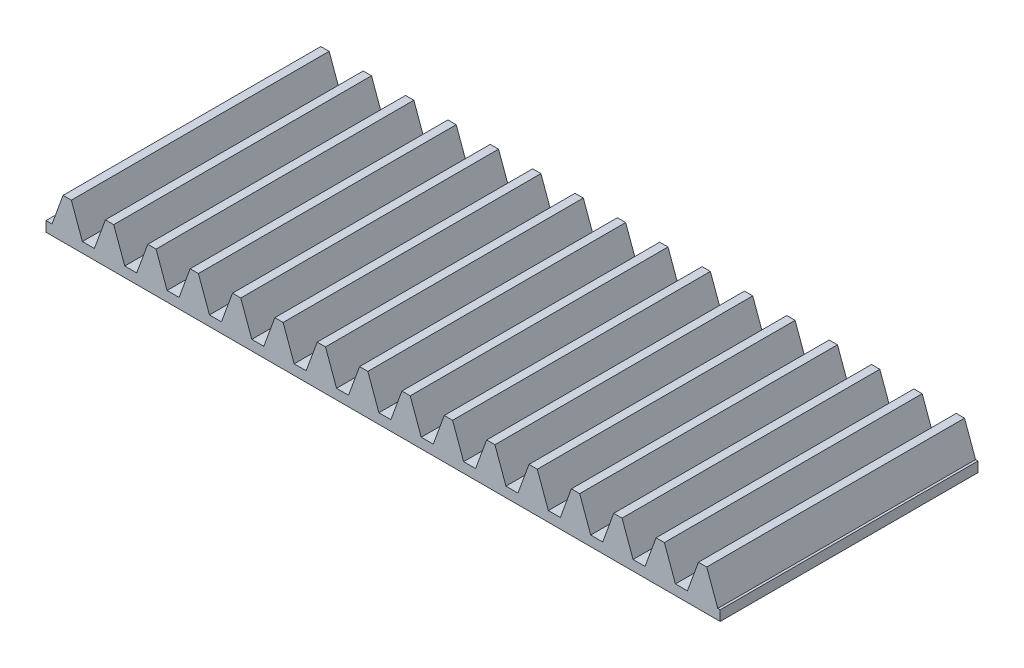
SolidWorks part; units mm, degrees
extrude "Blank" add sketch "BlankSke" against normal blind 19.12
sketch "BlankSke" plane through (0, 0, 0) normal (0, 0, 1) x (1, 0, 0)
  line L1 (0, 0) -> (50, 0)
  line L2 (0, 0) -> (0, 3)
  line L3 (0, 3) -> (50, 3)
  line L4 (50, 0) -> (50, 3)
  dimension "Length" = 50
  dimension "Blank_height" = 3
ref_plane "Plane1" through (0, 0, 0) normal (0, 0, 1) x (1, 0, 0)
ref_plane "Plane2" through (0, 0, 0) normal (0, 1, 0) x (1, 0, 0)
ref_plane "Plane3" through (0, 0, 0) normal (1, 0, 0) x (0, 0, -1)
sketch "HoldingSke" plane through (0, 0, 0) normal (0, 1, 0) x (1, 0, 0)
  line L0 (0, 0) -> (0.1392, 0.9903)
  line L1 (-15, 0) -> (100, 0) construction
  line L2 (0, 0) -> (-2.1039, 2.3779)
  line L3 (0, 0) -> (-11.863, 4.5341)
  line L4 (0, 0) -> (8.2587, 2.5249)
  line L5 (0, 0) -> (-23.7986, -8.8762)
  line L6 (0, 0) -> (-10.5278, -7.1032)
  line L9 (-71.009, 38.7566) -> (-24.0243, 55.8576)
  line L10 (-76.2, 3.3779) -> (-74.2, 3.3779)
  line L11 (0, 0) -> (-19.12, 0)
  line L12 (-76.2, 101.6) -> (-76.162, 101.6)
  line L13 (24.9733, 27.94) -> (52.9518, 28.4284)
  line L14 (24.9733, 27.94) -> (24.9743, 27.94)
  line L15 (24.9733, 27.94) -> (100.4006, 29.5858)
  circle A0 centre (0, 0) radius 19.05
  circle A1 centre (0, 0) radius 1
  circle A2 centre (0, 0) radius 12.7
  dimension "MPH" = 2
  dimension "Diameter" = 38.1
  dimension "Num_teeth" = 17
  dimension "Pitch" = 1
  dimension "Show_teeth" = 998
  dimension "Thickness" = 12.7
  dimension "Ap" = 20
  dimension "Pitch_height" = 2
  dimension "Width" = 19.12
  dimension "Backlash" = 0.038
  dimension "Addendum_fac" = 1
  dimension "Dedendum_fac" = 1.25
  dimension "Clearance_fac" = 0.25
  dimension "Dedendum_add" = 0.001
  dimension "Length" = 50
  dimension "Module" = 1
sketch "TooCutSkeIll" plane through (0, 0, 0) normal (0, 0, 1) x (1, 0, 0)
  line L0 (-1.2538, 2.9737) -> (-0.5045, 0.9152)
  line L1 (-0.2687, 0.75) -> (0.2687, 0.75)
  line L2 (0.5045, 0.9152) -> (1.2538, 2.9737)
  line L3 (50, 3) -> (0, 3) construction
  line L4 (0, 0) -> (0, 64.897) construction
  line L5 (-13.208, 2) -> (12.954, 2) construction
  line L6 (0, 0) -> (50, 0) construction
  line L7 (0.8994, 2) -> (0.8994, 48.7463) construction
  line L8 (-0.8994, 2) -> (-0.8994, 48.7463) construction
  line L9 (1.2914, 3) -> (1.2914, 3.0254)
  line L10 (-1.2914, 3) -> (-1.2914, 3.0254)
  line L11 (-1.2914, 3.0254) -> (1.2914, 3.0254)
  arc A0 (0.2687, 0.75) -> (0.5045, 0.9152) centre (0.2687, 1.001) ccw
  arc A1 (-0.5045, 0.9152) -> (-0.2687, 0.75) centre (-0.2687, 1.001) ccw
  arc A2 (1.2914, 3) -> (1.2538, 2.9737) centre (1.2914, 2.96) ccw
  arc A3 (-1.2538, 2.9737) -> (-1.2914, 3) centre (-1.2914, 2.96) ccw
  dimension "Pitch_height" = 2
  dimension "Addendum_plus" = 1.0254
  dimension "Pressure_angle" = 20
  dimension "Gap_width" = 1.7988
  dimension "Dedendum" = 1.25
extrude "ToothCutIll" [suppressed] cut sketch "TooCutSkeIll" against normal through all
sketch "TooCutSkeSim" plane through (0, 0, 0) normal (0, 0, 1) x (1, 0, 0)
  line L0 (0.4444, 0.75) -> (-0.4444, 0.75)
  line L1 (1.2726, 3.0254) -> (0.4444, 0.75)
  line L2 (0, 17.4625) -> (0, 53.467) construction
  line L3 (1.2726, 3.0254) -> (-1.2726, 3.0254)
  line L6 (-1.2726, 3.0254) -> (-0.4444, 0.75)
  line L9 (-0.8994, 2) -> (0.8994, 2) construction
  line L10 (0, 0) -> (50, 0) construction
  line L11 (0.8994, 2) -> (0.8994, 53.467) construction
  line L12 (-0.8994, 2) -> (-0.8994, 53.467) construction
  dimension "Pitch_height" = 2
  dimension "Addendum_plus" = 1.0254
  dimension "Pressure_angle" = 20
  dimension "Gap_width" = 1.7988
  dimension "Dedendum" = 1.25
extrude "ToothCutSim" cut sketch "TooCutSkeSim" against normal through all
pattern_linear "TeethCuts" count 17 spacing 3.1416 along (1, 0, 0) of "ToothCutIll", "ToothCutSim"
equation "' \"Module@HoldingSke\" = 6.35"
equation "' \"Num_teeth@HoldingSke\" = 12"
equation "' \"Ap@HoldingSke\" =  20"
equation "' \"Ap@HoldingSke\" = 20"
equation "' \"Width@HoldingSke\" = 0.25 * 25.4"
equation "' \"Show_teeth@HoldingSke\" = 500"
equation "' \"Backlash@HoldingSke\" = 0.009 * 25.4"
equation "' \"Addendum_fac@HoldingSke\" = 1.0"
equation "' \"Dedendum_fac@HoldingSke\" = 1.25"
equation "' \"Dedendum_add@HoldingSke\" = 0.00005 * 25.4"
equation "' \"Clearance_fac@HoldingSke\" = 0.25"
equation "' \"Pitch_height@HoldingSke\" = 1 * 25.4"
equation "' \"Length@HoldingSke\" = 4.71 * 25.4"
equation "\"Pitch@HoldingSke\" = 1 / \"Module@HoldingSke\""
equation "\"MPH@HoldingSke\" = \"Dedendum_fac@HoldingSke\" / \"Pitch@HoldingSke\" + 2 * \"Dedendum_add@HoldingSke\" + 0.002 * 25.4"
equation "\"MPH@HoldingSke\" = ((sgn( \"MPH@HoldingSke\" - \"Pitch_height@HoldingSke\")+1)*( \"MPH@HoldingSke\" - \"Pitch_height@HoldingSke\"))/2 + \"Pitch_height@HoldingSke\""
equation "\"Blank_height@BlankSke\" = \"Pitch_height@HoldingSke\" + \"Addendum_fac@HoldingSke\"  / \"Pitch@HoldingSke\" "
equation "\"Length@BlankSke\" =  \"Length@HoldingSke\""
equation "\"Face_width@Blank\" = \"Width@HoldingSke\""
equation "\"Pressure_angle@TooCutSkeIll\" = \"Ap@HoldingSke\""
equation "\"Addendum_plus@TooCutSkeIll\" =  \"Addendum_fac@HoldingSke\"  / \"Pitch@HoldingSke\" + 0.001 *25.4"
equation "\"Dedendum@TooCutSkeIll\" = \"Dedendum_fac@HoldingSke\"  / \"Pitch@HoldingSke\""
equation "\"Pitch_height@TooCutSkeIll\" =  \"MPH@HoldingSke\""
equation "\"Gap_width@TooCutSkeIll\" = 3.14159265 / 2 / \"Pitch@HoldingSke\" + 6 * \"Backlash@HoldingSke\""
equation "\"Pressure_angle@TooCutSkeSim\" = \"Ap@HoldingSke\""
equation "\"Addendum_plus@TooCutSkeSim\" =  \"Addendum_fac@HoldingSke\"  / \"Pitch@HoldingSke\" + 0.001 * 25.4"
equation "\"Dedendum@TooCutSkeSim\" = \"Dedendum_fac@HoldingSke\"  / \"Pitch@HoldingSke\""
equation "\"Pitch_height@TooCutSkeSim\" =  \"MPH@HoldingSke\""
equation "\"Gap_width@TooCutSkeSim\" = 3.14159265 / 2 / \"Pitch@HoldingSke\" + 6 * \"Backlash@HoldingSke\""
equation "\"Root_fillet@TooCutSkeIll\" = \"Clearance_fac@HoldingSke\" / \"Pitch@HoldingSke\" + \"Dedendum_add@HoldingSke\""
equation "\"Break_rad@TooCutSkeIll\" = 0.02 / \"Pitch@HoldingSke\" * 2"
equation "\"Linear_pitch@TeethCuts\" = 3.14159265 / \"Pitch@HoldingSke\""
equation "\"Num_teeth@HoldingSke\" = int( ( \"Length@HoldingSke\" + 0 ) / (3.14159265 / \"Pitch@HoldingSke\")) + 0.9999  + 1"
equation " \"Num_teeth@TeethCuts\" = int( \"Show_teeth@HoldingSke\" ) + 1"
equation " \"Num_teeth@TeethCuts\" = ((sgn( \"Num_teeth@TeethCuts\" - \"Num_teeth@HoldingSke\" )-1)*( \"Num_teeth@TeethCuts\" - \"Num_teeth@HoldingSke\" ))/-2+ \"Num_teeth@HoldingSke\""
equation " \"Num_teeth@TeethCuts\" = ((sgn( \"Num_teeth@TeethCuts\" - 2.0)+1)*( \"Num_teeth@TeethCuts\" - 2.0))/2 +2.0"
